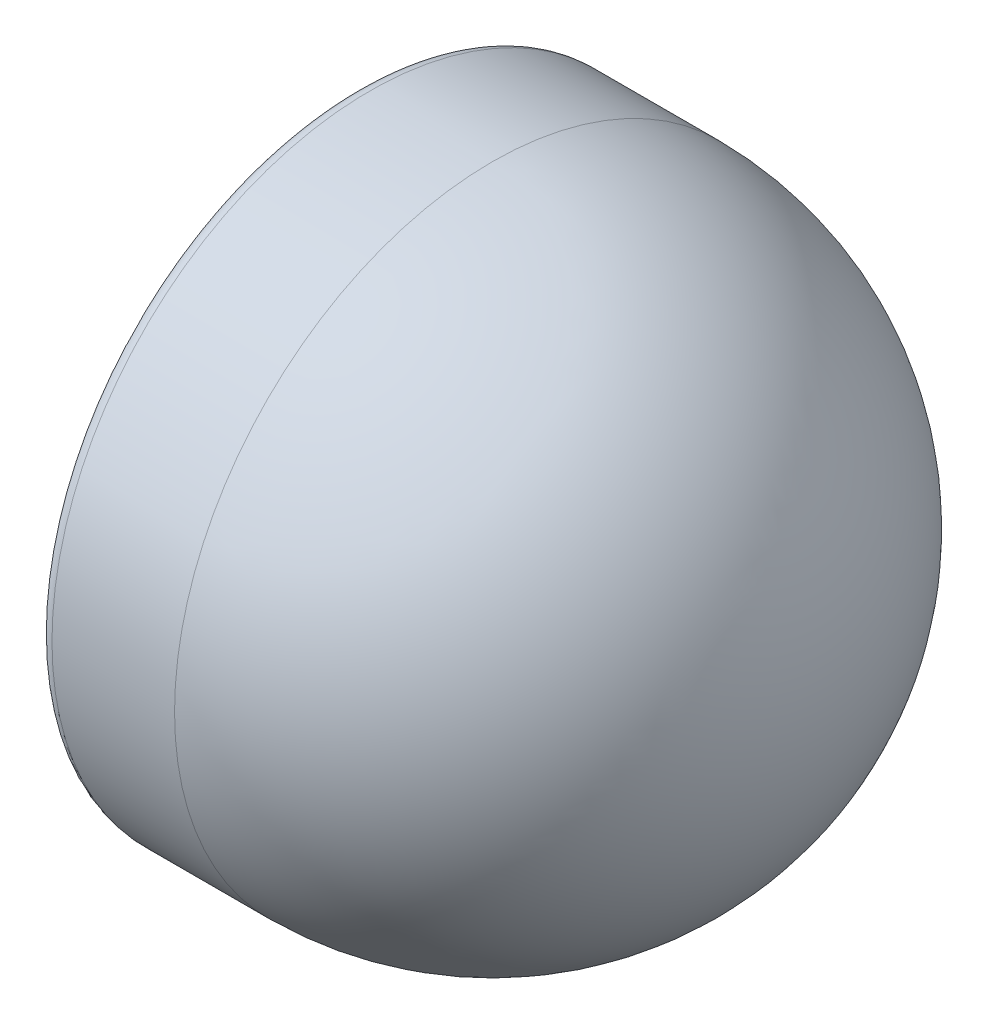
SolidWorks part; units mm, degrees
ref_plane "Front Plane" through (0, 0, 0) normal (0, 0, 1) x (1, 0, 0)
ref_plane "Top Plane" through (0, 0, 0) normal (0, 1, 0) x (1, 0, 0)
ref_plane "Right Plane" through (0, 0, 0) normal (1, 0, 0) x (0, 0, -1)
sketch "Sketch1" plane through (0, 0, 0) normal (0, 0, 1) x (1, 0, 0)
  line L0 (-70, 0) -> (72.5714, 0) construction
  line L1 (-70, 70) -> (-97, 70)
  line L2 (-100, 67) -> (-100, 61.5)
  line L3 (-98.5, 60) -> (-96.6213, 60)
  line L4 (-95.5607, 60.4393) -> (-92, 64)
  line L5 (-70, 69) -> (-97, 69)
  line L6 (-99, 67) -> (-99, 61.5)
  line L7 (-98.5, 61) -> (-96.6213, 61)
  line L8 (-96.2678, 61.1464) -> (-92.7071, 64.7071)
  line L9 (-92, 64) -> (-92, 64.7071)
  line L10 (-92, 64.7071) -> (-92.7071, 64.7071)
  line L11 (-1, 0) -> (0, 0)
  arc A0 (0, 0) -> (-70, 70) centre (-70, 0) ccw
  arc A1 (-97, 70) -> (-100, 67) centre (-97, 67) ccw
  arc A2 (-95.5607, 60.4393) -> (-96.6213, 60) centre (-96.6213, 61.5) cw
  arc A3 (-98.5, 60) -> (-100, 61.5) centre (-98.5, 61.5) cw
  arc A4 (-1, 0) -> (-70, 69) centre (-70, 0) ccw
  arc A5 (-97, 69) -> (-99, 67) centre (-97, 67) ccw
  arc A6 (-98.5, 61) -> (-99, 61.5) centre (-98.5, 61.5) cw
  arc A7 (-96.2678, 61.1464) -> (-96.6213, 61) centre (-96.6213, 61.5) cw
  point P13 (-100, 70)
  point P16 (-96, 60)
  point P19 (-100, 60)
  dimension "D1" = 70
  dimension "D7" = 3
  dimension "D8" = 1.5
  dimension "D2" = 10
  dimension "D3" = 30
  dimension "D4" = 4
  dimension "D5" = 135
  dimension "D6" = 70
  dimension "D10" = 7
  dimension "D9" = 1
revolve "Revolve1" add sketch "Sketch1" angle 360 about L0
